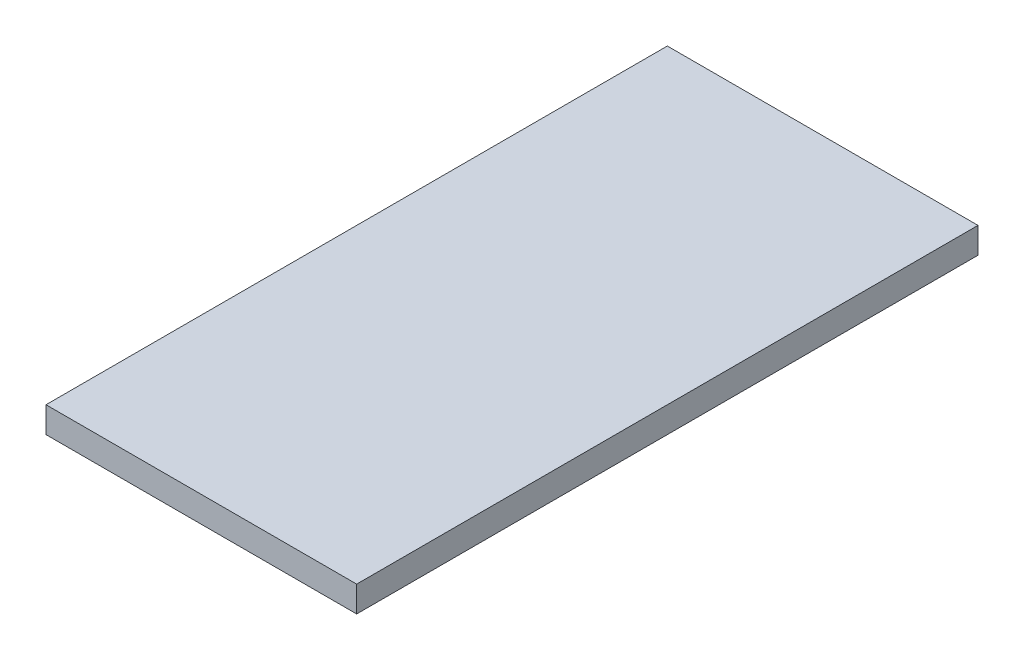
SolidWorks part; units mm, degrees
ref_plane "Plane1" through (0, 0, 0) normal (0, 0, 1) x (1, 0, 0)
ref_plane "Plane2" through (0, 0, 0) normal (0, 1, 0) x (1, 0, 0)
ref_plane "Plane3" through (0, 0, 0) normal (1, 0, 0) x (0, 0, -1)
sketch "Sketch1" plane through (0, 0, 0) normal (0, 1, 0) x (1, 0, 0)
  line L1 (0, 0) -> (120, 0)
  line L2 (0, 0) -> (0, 240)
  line L3 (0, 240) -> (120, 240)
  line L4 (120, 0) -> (120, 240)
  dimension "D1" = 120
  dimension "D2" = 240
extrude "Boss-Extrude1" add sketch "Sketch1" along normal blind 10
